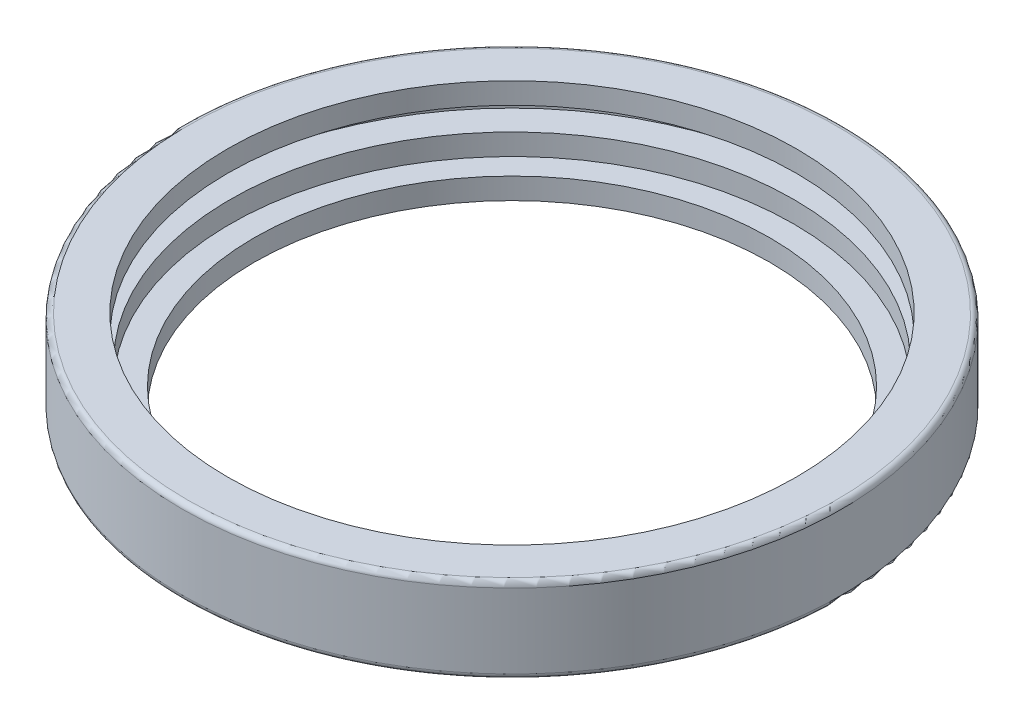
SolidWorks part; units mm, degrees
ref_plane "Front" through (0, 0, 0) normal (0, 0, 1) x (1, 0, 0)
ref_plane "Top" through (0, 0, 0) normal (0, 1, 0) x (1, 0, 0)
ref_plane "Right" through (0, 0, 0) normal (1, 0, 0) x (0, 0, -1)
sketch "Sketch1" plane through (0, 0, 0) normal (0, 0, 1) x (1, 0, 0)
  line L0 (0, 0) -> (0, 33.7544) construction
  line L1 (24.25, 0) -> (31, 0)
  line L2 (31, 0) -> (31, 8)
  line L3 (31, 8) -> (26.75, 8)
  line L4 (26.75, 8) -> (26.75, 6)
  line L5 (26.75, 6) -> (29.25, 6)
  line L6 (29.25, 6) -> (29.25, 4)
  line L7 (29.25, 4) -> (26.5, 4)
  line L8 (26.5, 4) -> (26.5, 2)
  line L9 (26.5, 2) -> (24.25, 2)
  line L10 (24.25, 2) -> (24.25, 0)
  dimension "D1" = 62
  dimension "D2" = 48.5
  dimension "D3" = 53.5
  dimension "D4" = 53
  dimension "D5" = 2
  dimension "D6" = 2
  dimension "D7" = 8
  dimension "D8" = 2
  dimension "D9" = 58.5
revolve "Revolve1" add sketch "Sketch1" angle 360 about L0
fillet "Fillet1" radius 0.5 2 edges at (0, 0, -31) (0, 8, -31)
